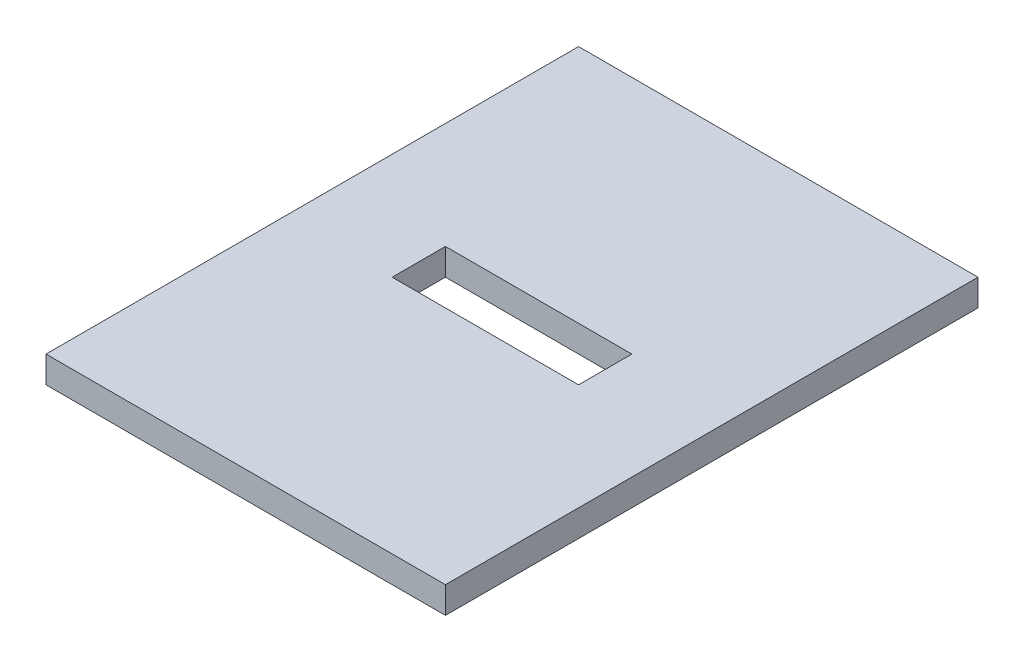
SolidWorks part; units mm, degrees
material "AL MG SI 0.5 / 6060"
ref_plane "Vorne" through (0, 0, 0) normal (0, 0, 1) x (1, 0, 0)
ref_plane "Oben" through (0, 0, 0) normal (0, 1, 0) x (1, 0, 0)
ref_plane "Rechts" through (0, 0, 0) normal (1, 0, 0) x (0, 0, -1)
sketch "D" plane through (0, 0, 0) normal (0, 1, 0) x (1, 0, 0)
  line L0 (-5.5, 0) -> (5.5, 0) construction
  line L3 (0, 0) -> (0, 40) construction
  line L4 (0, 40) -> (10, 60) construction
  line L5 (10, 60) -> (10, 0) construction
  point P1 (49.9844, 28.7514)
  point P2 (8.9108, 0)
  point P8 (33.1726, 0)
  point P14 (0, 0)
  point P15 (0, 0)
  dimension "D1" = 10
  dimension "D2" = 40
  dimension "D3" = 60
sketch "Skizze1" plane through (0, 0, 0) normal (0, 1, 0) x (1, 0, 0)
  line L0 (-5.5, 0) -> (5.5, 0) construction
  line L1 (-50, -50) -> (100, -50)
  line L2 (-50, -50) -> (-50, 150)
  line L3 (-50, 150) -> (100, 150)
  line L4 (100, -50) -> (100, 150)
  line L5 (0, -5.5) -> (0, 5.5) construction
  dimension "D1" = 50
  dimension "D2" = 50
  dimension "D3" = 150
  dimension "D4" = 200
extrude "Aufsatz-Linear austragen1" add sketch "Skizze1" along normal blind 10
sketch "Skizze2" plane through (0, 0, 0) normal (0, -1, 0) x (1, 0, 0)
  line L0 (0, -5.5) -> (0, 5.5) construction
  line L1 (-10, -40) -> (60, -40)
  line L2 (-10, -40) -> (-10, -60)
  line L3 (-10, -60) -> (60, -60)
  line L4 (60, -40) -> (60, -60)
  point P4 (-31.6755, 75.1824)
  dimension "D1" = 10
  dimension "D3" = 20
  dimension "D4" = 70
extrude "Schnitt-Linear austragen2" cut sketch "Skizze2" against normal through all both and the other way through all
